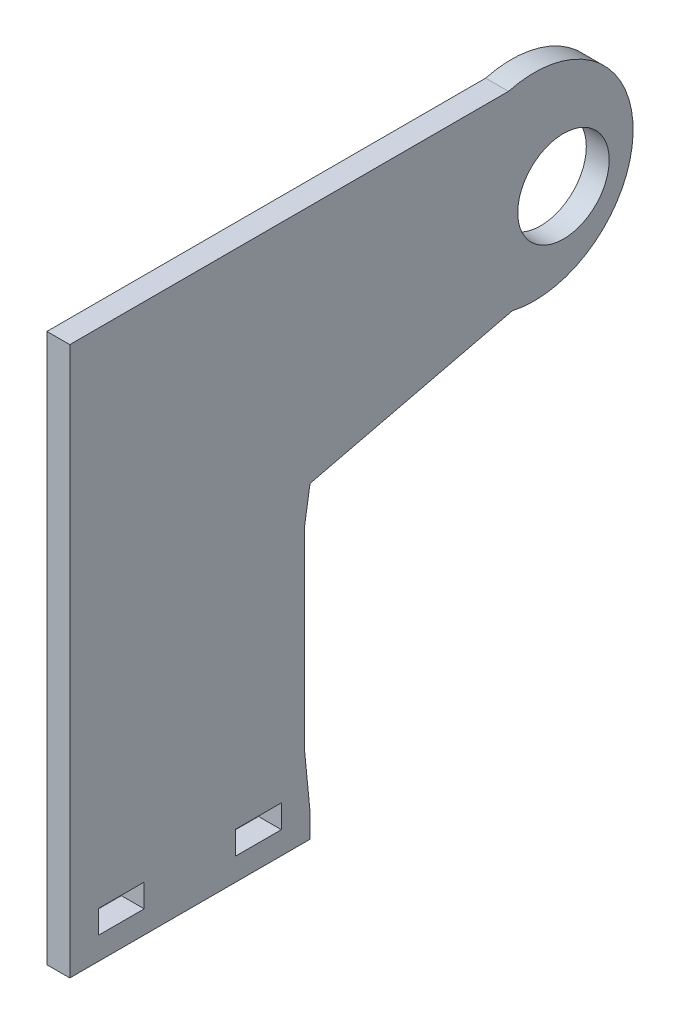
SolidWorks part; units mm, degrees
ref_plane "Front Plane" through (0, 0, 0) normal (0, 0, 1) x (1, 0, 0)
ref_plane "Top Plane" through (0, 0, 0) normal (0, 1, 0) x (1, 0, 0)
ref_plane "Right Plane" through (0, 0, 0) normal (1, 0, 0) x (0, 0, -1)
sketch "Sketch1" plane through (0, 0, 0) normal (1, 0, 0) x (0, 0, -1)
  line L0 (20.3087, 40.6173) -> (43.1578, 40.6173)
  line L1 (-17.7913, -35.5827) -> (15.586, -35.5827)
  line L2 (-17.7913, -35.5827) -> (-17.7913, 40.6173)
  line L3 (-17.7913, 40.6173) -> (20.3087, 40.6173)
  line L4 (15.586, -35.5827) -> (15.586, 7.2284)
  line L5 (-17.7913, -35.5827) -> (20.3087, 40.6173) construction
  line L6 (-17.7913, 40.6173) -> (15.586, -35.5827) construction
  line L8 (43.6922, 13.9487) -> (15.586, 7.2284)
  arc A0 (43.1578, 40.6173) -> (43.6922, 13.9487) centre (46.7287, 27.3492) cw
  point P0 (0, 0)
  dimension "D1" = 38.1
  dimension "D2" = 76.2
extrude "Boss-Extrude1" add sketch "Sketch1" along normal blind 3.175
sketch "Sketch2" plane through (3.175, 0, 0) normal (1, 0, 0) x (0, 0, -1)
  line L0 (-17.7913, -35.5827) -> (15.586, -35.5827) construction
  line L1 (-17.7913, 40.6173) -> (-17.7913, -35.5827) construction
  line B0 (-5.0913, -19.0727) -> (15.4947, -19.0727)
  line B1 (15.4947, -19.0727) -> (15.4947, 22.2023)
  line B2 (15.4947, 22.2023) -> (-5.0913, 22.2023)
  line B3 (-5.0913, 22.2023) -> (-5.0913, -19.0727)
  circle B4 centre (10.1567, 27.0283) radius 1.7145
  circle B5 centre (0.2467, 27.0283) radius 1.7145
  circle B6 centre (10.0555, -23.8987) radius 1.7145
  circle B7 centre (0.1455, -23.8987) radius 1.7145
  line B8 (10.1567, 27.0283) -> (10.0555, -23.8987) construction
  dimension "D1" = 16.51
  dimension "D2" = 12.7
sketch_block_instance "block_servo_holes_standard-1"
sketch_block "block_servo_holes_standard" parameters "D1"=3.429, "D2"=3.429, "D3"=3.429, "D4"=3.429, "D5"=3.429, "D6"=13.1735, "D7"=41.336, "D8"=20.586, "D9"=20.586, "D10"=50.292
sketch "Sketch3" plane through (3.175, 0, 0) normal (1, 0, 0) x (0, 0, -1)
  line L0 (43.1578, 40.6173) -> (-17.7913, 40.6173) construction
  line L2 (-17.7913, 40.6173) -> (-17.7913, -35.5827) construction
  circle A0 centre (50.7887, 25.3773) radius 6.35
  dimension "D1" = 15.24
  dimension "D2" = 68.58
extrude "Cut-Extrude2" cut sketch "Sketch3" against normal through all
sketch "Sketch4" plane through (3.175, 0, 0) normal (1, 0, 0) x (0, 0, -1)
  line L0 (-1.1026, -35.5827) -> (-1.1026, -30.8202) construction
  line L1 (-13.8026, -32.4331) -> (-7.4526, -32.4331)
  line L2 (-13.8026, -32.4331) -> (-13.8026, -29.2073)
  line L3 (-13.8026, -29.2073) -> (-7.4526, -29.2073)
  line L4 (-7.4526, -32.4331) -> (-7.4526, -29.2073)
  line L5 (-13.8026, -32.4331) -> (-7.4526, -29.2073) construction
  line L6 (-13.8026, -29.2073) -> (-7.4526, -32.4331) construction
  line L7 (5.2474, -32.4331) -> (11.5974, -32.4331)
  line L8 (5.2474, -32.4331) -> (5.2474, -29.2073)
  line L9 (5.2474, -29.2073) -> (11.5974, -29.2073)
  line L10 (11.5974, -32.4331) -> (11.5974, -29.2073)
  line L11 (5.2474, -32.4331) -> (11.5974, -29.2073) construction
  line L12 (5.2474, -29.2073) -> (11.5974, -32.4331) construction
  line L13 (-17.7913, -35.5827) -> (15.586, -35.5827) construction
  line L14 (-1.1026, -30.8202) -> (-7.4526, -30.8202) construction
  line L15 (-1.1026, -30.8202) -> (5.2474, -30.8202) construction
  point P0 (-10.6276, -30.8202)
  point P5 (8.4224, -30.8202)
  dimension "D1" = 6.35
  dimension "D2" = 4.7625
  dimension "D3" = 6.35
  dimension "D4" = 6.35
  dimension "D5" = 3.2258
  dimension "D6" = 3.2258
sketch "Sketch5" plane through (0, 0, 0) normal (-1, 0, 0) x (0, 0, 1)
  line L0 (-15.586, 7.2284) -> (-14.847, 2.5785)
  line L1 (-14.847, 2.5785) -> (-14.847, -24.7243)
  line L2 (-14.847, -24.7243) -> (-15.586, -32.2734)
  line L3 (-15.586, -35.5827) -> (-15.586, 7.2284) construction
  line L4 (-15.586, -32.2734) -> (-15.586, 7.2284)
extrude "Cut-Extrude4" cut sketch "Sketch5" against normal through all
extrude "Cut-Extrude3" cut sketch "Sketch4" against normal through all
